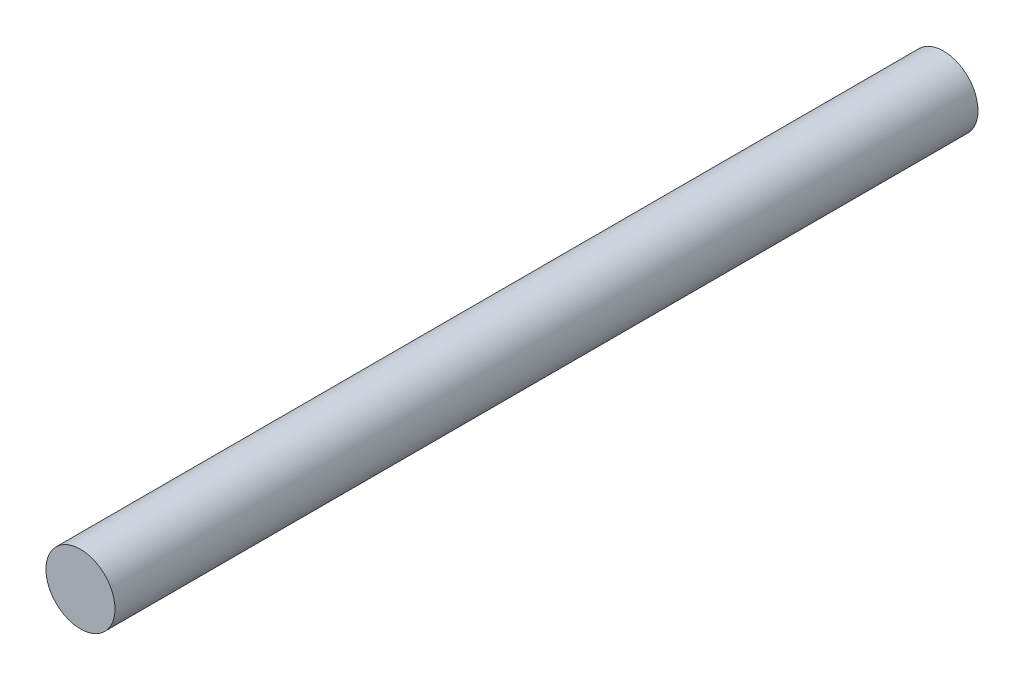
SolidWorks part; units mm, degrees
ref_plane "Ebene vorne" through (0, 0, 0) normal (0, 0, 1) x (1, 0, 0)
ref_plane "Ebene oben" through (0, 0, 0) normal (0, 1, 0) x (1, 0, 0)
ref_plane "Ebene rechts" through (0, 0, 0) normal (1, 0, 0) x (0, 0, -1)
sketch "Skizze1" plane through (0, 0, 0) normal (0, 0, 1) x (1, 0, 0)
  circle A0 centre (0, 0) radius 10
extrude "Aufsatz-Linear austragen1" add sketch "Skizze1" along normal blind 250
